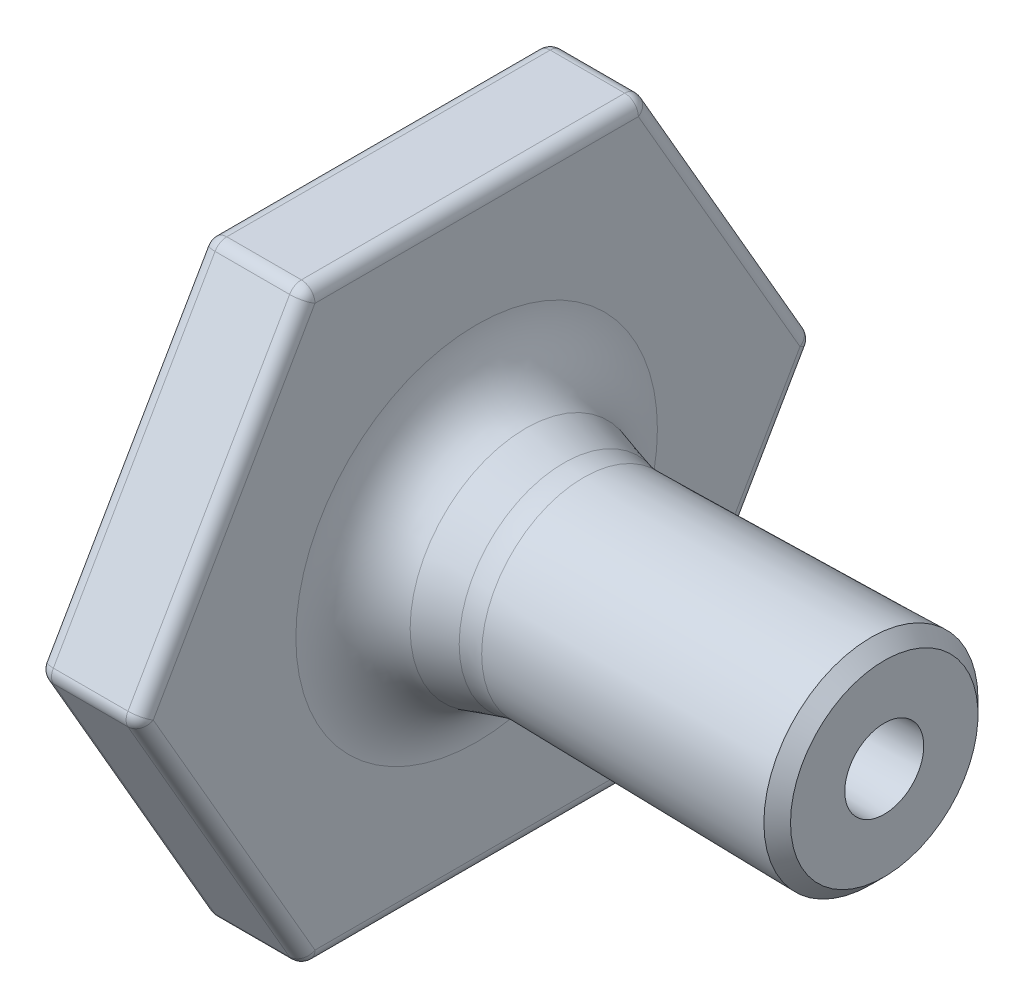
SolidWorks part; units mm, degrees
ref_plane "Front Plane" through (0, 0, 0) normal (0, 0, 1) x (1, 0, 0)
ref_plane "Top Plane" through (0, 0, 0) normal (0, 1, 0) x (1, 0, 0)
ref_plane "Right Plane" through (0, 0, 0) normal (1, 0, 0) x (0, 0, -1)
sketch "Sketch1" plane through (0, 0, 0) normal (0, 0, 1) x (1, 0, 0)
  line L0 (0, 1.825) -> (6.7189, 1.825)
  line L1 (0, -55) -> (0, 55) construction
  line L2 (6.7189, 1.825) -> (9.596, 1)
  line L4 (9.596, 1) -> (19.0231, 1.1645)
  line L8 (55, 0) -> (-55, 0) construction
  line L9 (0, 0) -> (19.0231, 0) construction
  line L10 (19.0231, 1.1645) -> (19.0231, 0) construction
  line L11 (0, 3.825) -> (7, 3.825) construction
  line L12 (7, 3.825) -> (9.86, 3.0049)
  line L13 (9.86, 3.0049) -> (19.0231, 3.1649)
  line L14 (0, 0) -> (0, 1.825) construction
  line L15 (19.0231, 1.1645) -> (10.4502, 1.1646) construction
  line L16 (0, 1.825) -> (0, 2.625)
  line L17 (7, 3.825) -> (7, 10)
  line L18 (7, 10) -> (4, 10)
  line L19 (4, 10) -> (4, 2.625)
  line L20 (0, 2.625) -> (4, 2.625)
  line L21 (0, 2.625) -> (0, 3.825) construction
  line L22 (9.86, 3.0049) -> (18.9882, 3.1642) construction
  line L23 (19.0231, 1.1645) -> (19.0231, 3.1649)
  dimension "D1" = 1
  dimension "D2" = 1.1645
  dimension "D3" = 2
  dimension "D4" = 2.625
  dimension "D5" = 0.8
  dimension "D6" = 3
  dimension "D7" = 16
  dimension "D8" = 1
  dimension "D9" = 10
  dimension "D10" = 4
revolve "Revolve1" add sketch "Sketch1" angle 360 about L9
fillet "Fillet4" radius 3 2 edges at (9.596, 0, 1) (6.7189, 0, 1.825)
chamfer "Chamfer1" distance 0.4 angle 45 1 edges at (19.0231, 0, 3.1649)
sketch "Sketch2" plane through (7, 0, 0) normal (1, 0, 0) x (0, 0, -1)
  line L0 (0, 0) -> (10, 0) construction
  line L1 (10, 0) -> (5, 8.6603)
  line L2 (5, 8.6603) -> (-5, 8.6603)
  line L3 (-5, 8.6603) -> (-10, 0)
  line L4 (-10, 0) -> (-5, -8.6603)
  line L5 (-5, -8.6603) -> (5, -8.6603)
  line L6 (5, -8.6603) -> (10, 0)
  circle A0 centre (0, 0) radius 8.6603 construction
  circle A1 centre (0, 0) radius 10 construction
  circle A2 centre (0, 0) radius 10
  circle M2 centre (0, 0) radius 10
extrude "Cut-Extrude1" cut sketch "Sketch2" against normal through all both and the other way through all contours L3 M2 | L2 M2 | L1 M2 | L4 M2 | L5 M2 | L6 M2
fillet "Fillet5" radius 0.4 18 edges at (5.5, 8.6603, -5) (5.5, 0, -10) (5.5, -8.6603, -5) (5.5, -8.6603, 5) (5.5, 0, 10) (5.5, 8.6603, 5) (4, -8.6603, 0) (4, -4.3301, 7.5) (4, 4.3301, -7.5) (4, -4.3301, -7.5) (4, 8.6603, 0) (4, 4.3301, 7.5) (7, 8.6603, 0) (7, 4.3301, -7.5) (7, -4.3301, -7.5) (7, -8.6603, 0) (7, -4.3301, 7.5) (7, 4.3301, 7.5)
fillet "Fillet6" radius 2 2 edges at (9.86, 0, 3.0049) (7, 0, 3.825)
